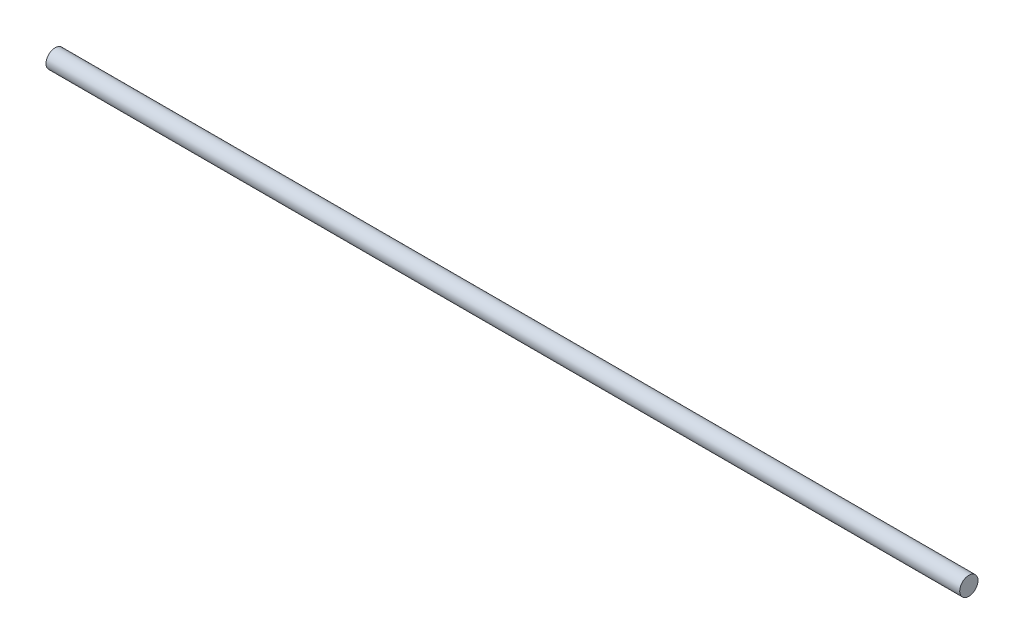
SolidWorks part; units mm, degrees
ref_plane "Front Plane" through (0, 0, 0) normal (0, 0, 1) x (1, 0, 0)
ref_plane "Top Plane" through (0, 0, 0) normal (0, 1, 0) x (1, 0, 0)
ref_plane "Right Plane" through (0, 0, 0) normal (1, 0, 0) x (0, 0, -1)
sketch "Sketch1" plane through (0, 0, 0) normal (0, 1, 0) x (1, 0, 0)
  line L0 (0, 0) -> (635, 0)
  dimension "D1" = 635
sweep "Sweep1" add path "Sketch1" circular profile diameter 12.7 parameters "D3"=12.7
